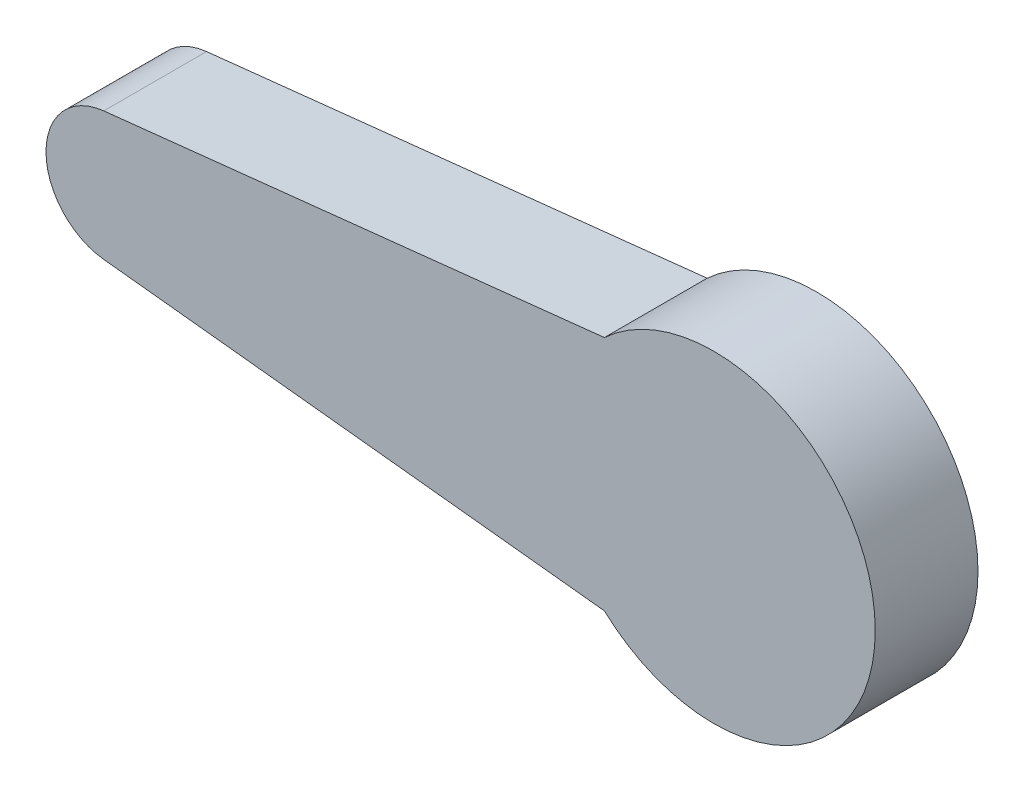
SolidWorks part; units mm, degrees
ref_plane "Front Plane" through (0, 0, 0) normal (0, 0, 1) x (1, 0, 0)
ref_plane "Top Plane" through (0, 0, 0) normal (0, 1, 0) x (1, 0, 0)
ref_plane "Right Plane" through (0, 0, 0) normal (1, 0, 0) x (0, 0, -1)
sketch "Sketch1" plane through (0, 0, 0) normal (0, 0, 1) x (1, 0, 0)
  line L0 (-2.3083, 2.4981) -> (9.375, 3.1901)
  line L1 (9.375, -3.1901) -> (-2.3083, -2.4981)
  spline S0 degree 3 poles (9.375, 3.1901) (9.7438, 3.5351) (10.5421, 3.8854) (11.7399, 4.0538) (12.7816, 3.904) (13.6476, 3.5884) (14.1725, 3.1236) (14.7494, 2.728) (15.2394, 2.0155) (15.6535, 1.0509) (15.789, -0.0007) (15.6517, -1.0481) (15.2469, -2.0252) (14.6033, -2.864) (13.7643, -3.5078) (12.7878, -3.9119) (11.7382, -4.0517) (10.5429, -3.8863) (9.7436, -3.5348) (9.375, -3.1901) knots 0 0 0 0 0.085137 0.144403 0.203669 0.262935 0.297503 0.322201 0.381468 0.440734 0.5 0.559266 0.618532 0.677799 0.737065 0.796331 0.855597 0.914863 1 1 1 1
  spline S1 degree 3 poles (-2.3083, -2.4981) (-2.7303, -2.4987) (-3.3653, -2.3178) (-4.0519, -1.7912) (-4.4545, -1.2665) (-4.7076, -0.6556) (-4.7939, 0) (-4.7076, 0.6556) (-4.4545, 1.2665) (-4.0519, 1.7912) (-3.3653, 2.3178) (-2.7303, 2.4987) (-2.3083, 2.4981) knots 0 0 0 0 0.162547 0.246911 0.331273 0.415637 0.5 0.584363 0.668727 0.753089 0.837453 1 1 1 1
sketch "Sketch2" plane through (0, 0, 0) normal (0, 0, 1) x (1, 0, 0)
  line L1 (7.9369, 4.6075) -> (-11.5502, 2.5042)
  line L4 (-11.5502, -2.5042) -> (7.9369, -4.6075)
  arc A3 (-11.5502, 2.5042) -> (-11.5502, -2.5042) centre (-11.2799, 0) ccw
  arc A4 (7.9369, 4.6075) -> (7.9369, -4.6075) centre (12.2014, 0) cw
  point P1 (-13.7986, 0)
  dimension "D1" = 26
extrude "Boss-Extrude6" add sketch "Sketch2" along normal blind 4 contours A4 L4 A3 L1
extrude "Cut-Extrude1" cut sketch "Sketch1" along normal blind 2
